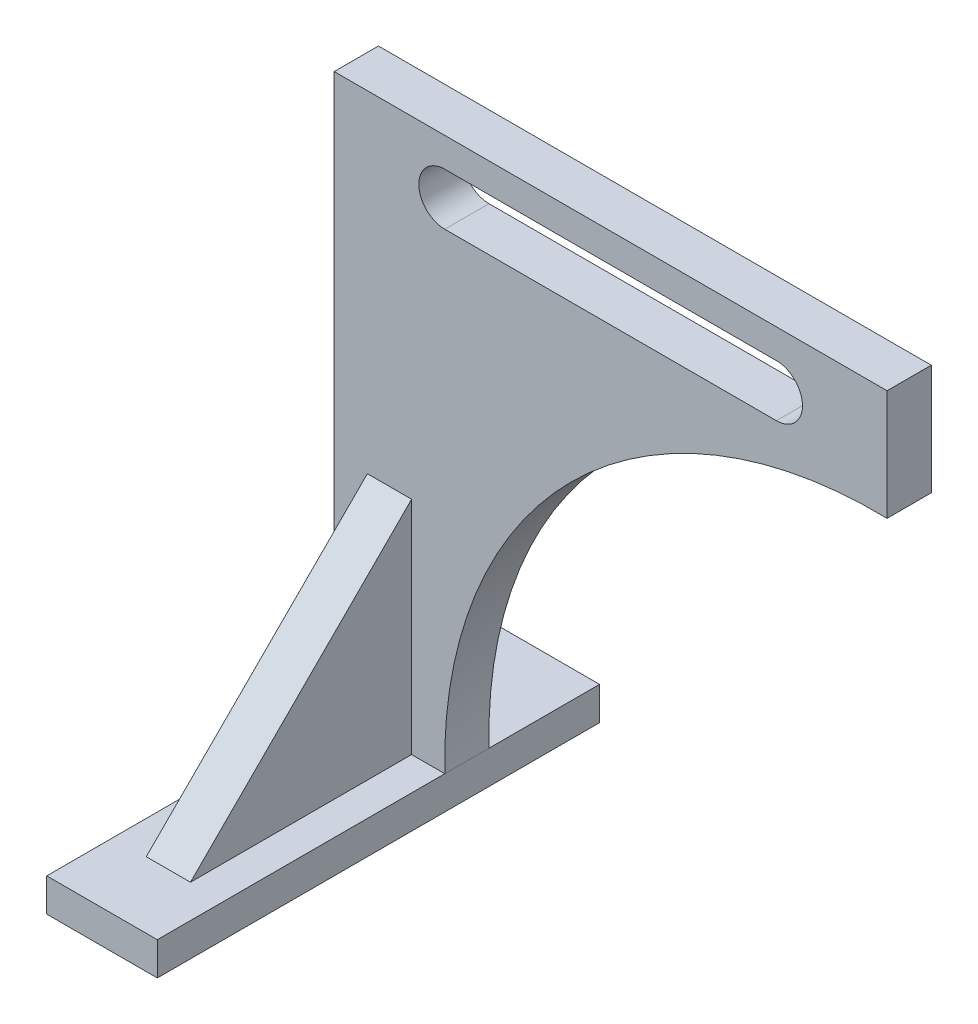
SolidWorks part; units mm, degrees
ref_plane "Front Plane" through (0, 0, 0) normal (0, 0, 1) x (1, 0, 0)
ref_plane "Top Plane" through (0, 0, 0) normal (0, 1, 0) x (1, 0, 0)
ref_plane "Right Plane" through (0, 0, 0) normal (1, 0, 0) x (0, 0, -1)
sketch "Sketch1" plane through (0, 0, 0) normal (0, 1, 0) x (1, 0, 0)
  line L1 (-25, 100) -> (25, 100)
  line L2 (-25, 100) -> (-25, -100)
  line L3 (-25, -100) -> (25, -100)
  line L4 (25, 100) -> (25, -100)
  line L5 (-25, 100) -> (25, -100) construction
  line L6 (-25, -100) -> (25, 100) construction
  point P0 (0, 0)
  dimension "D1" = 50
  dimension "D2" = 200
extrude "Boss-Extrude1" add sketch "Sketch1" along normal blind 15 contours L1 L4 L3 L2
ref_plane "Plane1" through (0, 0, -50) normal (0, 0, 1) x (1, 0, 0)
sketch "Sketch2" plane through (0, 0, -50) normal (0, 0, 1) x (1, 0, 0)
  line L0 (-25, 15) -> (-25, 265)
  line L1 (-25, 265) -> (225, 265)
  line L2 (225, 265) -> (225, 215)
  line L3 (-25, 15) -> (25, 15)
  line L4 (-25, 15) -> (25, 15) construction
  arc A0 (225, 215) -> (25, 15) centre (220.242, 19.758) ccw
  dimension "D5" = 195.3
  dimension "D1" = 50
  dimension "D2" = 250
  dimension "D3" = 250
  dimension "D4" = 50
extrude "Boss-Extrude2" add sketch "Sketch2" along normal blind 20
sketch "Sketch3" plane through (0, 0, 0) normal (1, 0, 0) x (0, 0, -1)
  line L0 (-70, 15) -> (30, 15)
  line L1 (30, 15) -> (-100, 15) construction
  line L2 (30, 15) -> (30, 115)
  line L3 (30, 215.058) -> (30, 15) construction
  line L4 (30, 115) -> (-70, 15)
  dimension "D1" = 100
  dimension "D2" = 100
extrude "Boss-Extrude3" add sketch "Sketch3" along normal mid plane 20
sketch "Sketch4" plane through (0, 0, -30) normal (0, 0, 1) x (1, 0, 0)
  line L0 (-25, 265) -> (-25, 15) construction
  line L1 (225, 215) -> (225, 265) construction
  line L2 (225, 265) -> (-25, 265) construction
  line L3 (25, 228.25) -> (175, 228.25)
  line L4 (25, 251.75) -> (175, 251.75)
  arc A0 (175, 228.25) -> (175, 251.75) centre (175, 240) ccw
  arc A1 (25, 251.75) -> (25, 228.25) centre (25, 240) ccw
  dimension "D2" = 23.5
  dimension "D3" = 50
  dimension "D4" = 50
  dimension "D6" = 25
extrude "Cut-Extrude1" cut sketch "Sketch4" against normal through all
